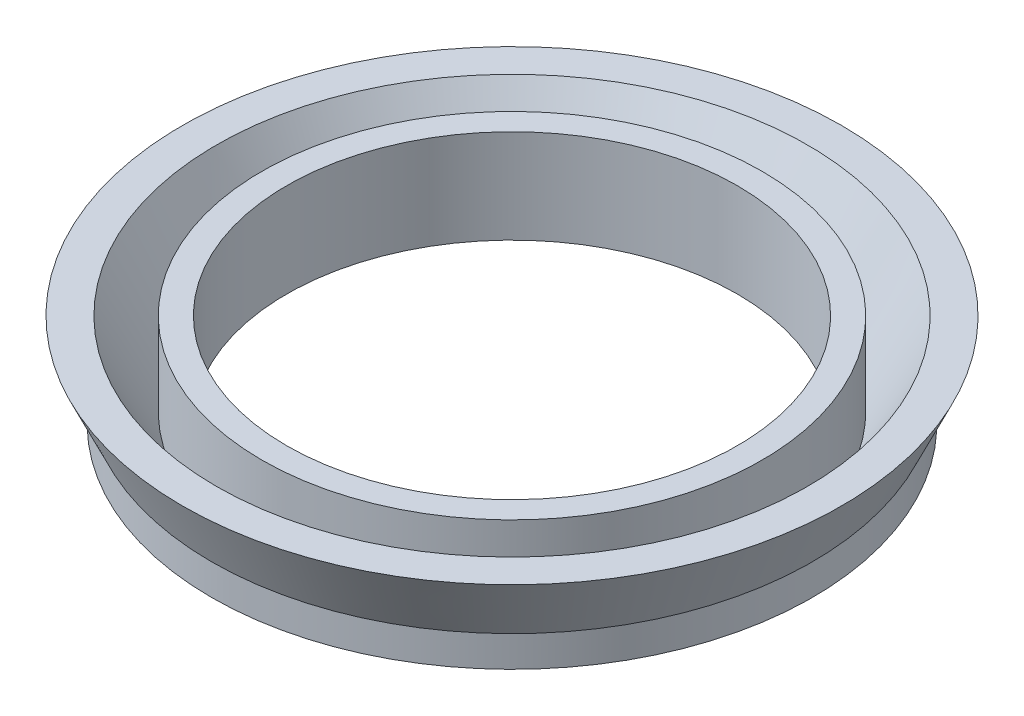
SolidWorks part; units mm, degrees
ref_plane "Alzado" through (0, 0, 0) normal (0, 0, 1) x (1, 0, 0)
ref_plane "Planta" through (0, 0, 0) normal (0, 1, 0) x (1, 0, 0)
ref_plane "Vista lateral" through (0, 0, 0) normal (1, 0, 0) x (0, 0, -1)
sketch "Croquis1" plane through (0, 0, 0) normal (0, 0, 1) x (1, 0, 0)
  line L0 (0, 18.7429) -> (0, -19.9314) construction
  line L1 (12, 0) -> (16, 0)
  line L2 (16, 0) -> (16, 1.6457)
  line L3 (16, 1.6457) -> (17.5525, 5)
  line L4 (15.747, 5) -> (13.3224, 0.5632)
  line L5 (17.5525, 5) -> (15.747, 5)
  line L6 (12, 0) -> (12, 5)
  line L7 (12, 5) -> (13.3224, 5)
  line L8 (13.3224, 5) -> (13.3224, 0.5632)
  dimension "D1" = 16
  dimension "D2" = 4
  dimension "D3" = 5
revolve "Revolución1" add sketch "Croquis1" angle 360 about L0
